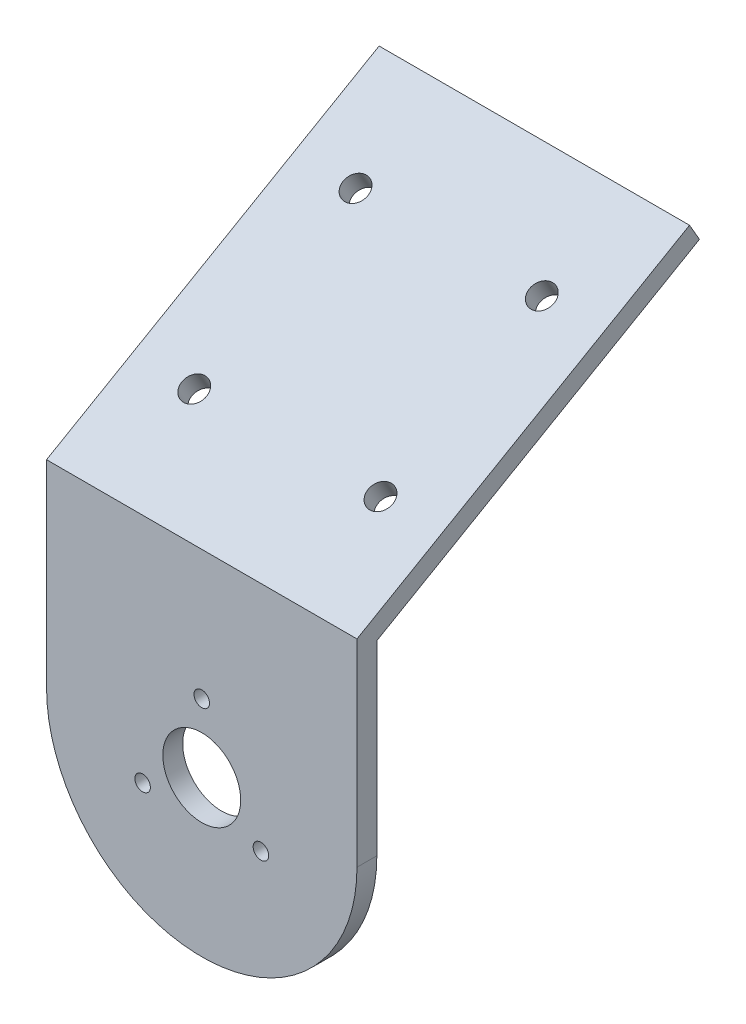
SolidWorks part; units mm, degrees
material "7075-T6 (SN)"
ref_plane "Front Plane" through (0, 0, 0) normal (0, 0, 1) x (1, 0, 0)
ref_plane "Top Plane" through (0, 0, 0) normal (0, 1, 0) x (1, 0, 0)
ref_plane "Right Plane" through (0, 0, 0) normal (1, 0, 0) x (0, 0, -1)
sketch "Sketch1" plane through (0, 0, 0) normal (0, 0, 1) x (1, 0, 0)
  line L0 (-25, 0) -> (-25, 30)
  line L1 (-25, 30) -> (25, 30)
  line L2 (25, 30) -> (25, 0)
  circle A0 centre (0, 0) radius 6.2732
  arc A1 (-25, 0) -> (25, 0) centre (0, 0) ccw
  circle A2 centre (0, 11) radius 1.25
  circle A3 centre (9.5263, -5.5) radius 1.25
  circle A4 centre (-9.5263, -5.5) radius 1.25
  circle A5 centre (0, 0) radius 11 construction
  dimension "D1" = 50
  dimension "D2" = 30
  dimension "D3" = 12.5465
  dimension "D4" = 2.5
  dimension "D5" = 2.5
  dimension "D6" = 2.5
extrude "Boss-Extrude1" add sketch "Sketch1" along normal up to surface (3.2 mm away)
sketch "Sketch2" plane through (25, 0, 0) normal (1, 0, 0) x (0, 0, -1)
  line L0 (0, 30) -> (51.9615, 60)
  line L1 (51.9615, 60) -> (50.3615, 62.7713)
  line L2 (50.3615, 62.7713) -> (-3.2, 31.8475)
  line L3 (-3.2, 31.8475) -> (-3.2, 30)
  line L4 (-3.2, 30) -> (0, 30)
  line L5 (0, 0) -> (0, 30) construction
  dimension "D1" = 3.2
  dimension "D2" = 60
  dimension "D3" = 120
extrude "Boss-Extrude2" add sketch "Sketch2" against normal up to surface (50 mm away) up to face at (-25, 15, 1.6)
sketch "Sketch3" plane through (0, 25.2713, 14.5904) normal (0, 0.866, 0.5) x (1, 0, 0)
  line L0 (-25, 75) -> (25, 75) construction
  line L1 (-15, 29.0762) -> (15, 29.0762) construction
  line L2 (-15, 29.0762) -> (-15, 59.0762) construction
  line L3 (-15, 59.0762) -> (15, 59.0762) construction
  line L4 (15, 29.0762) -> (15, 59.0762) construction
  line L5 (-15, 29.0762) -> (15, 59.0762) construction
  line L6 (-15, 59.0762) -> (15, 29.0762) construction
  line L7 (-25, 13.1525) -> (-25, 75) construction
  circle A0 centre (15, 59.0762) radius 2
  circle A1 centre (15, 29.0762) radius 2
  circle A2 centre (-15, 59.0762) radius 2
  circle A3 centre (-15, 29.0762) radius 2
  point P0 (0, 44.0762)
  point P8 (0, 75)
  point P12 (-25, 44.0762)
  dimension "D3" = 4
  dimension "D4" = 4
  dimension "D5" = 4
  dimension "D6" = 4
  dimension "D1" = 30
  dimension "D2" = 30
extrude "Cut-Extrude1" cut sketch "Sketch3" against normal up to next
